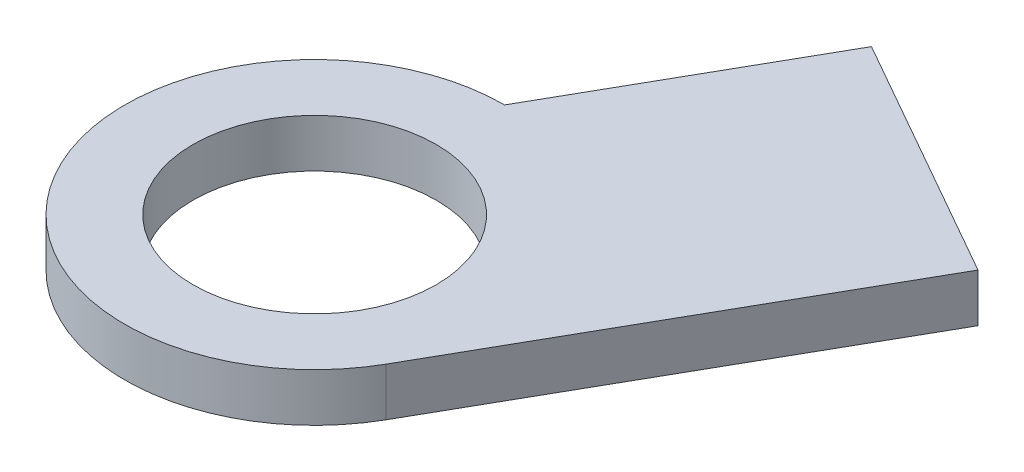
SolidWorks part; units mm, degrees
ref_plane "Front Plane" through (0, 0, 0) normal (0, 0, 1) x (1, 0, 0)
ref_plane "Top Plane" through (0, 0, 0) normal (0, 1, 0) x (1, 0, 0)
ref_plane "Right Plane" through (0, 0, 0) normal (1, 0, 0) x (0, 0, -1)
sketch "Sketch1" plane through (0, 0, 0) normal (0, 1, 0) x (1, 0, 0)
  circle A0 centre (0, 0) radius 12.5
  dimension "D2" = 25
extrude "Boss-Extrude1" add sketch "Sketch1" along normal blind 17.6
sketch "Sketch2" plane through (0, 17.6, 0) normal (0, 1, 0) x (1, 0, 0)
  circle A0 centre (0, 0) radius 5.5
  dimension "D1" = 11
extrude "Cut-Extrude1" cut sketch "Sketch2" against normal blind 50.8
sketch "Sketch3" plane through (0, 17.6, 0) normal (0, 1, 0) x (1, 0, 0)
  circle A0 centre (0, 0) radius 8
  dimension "D1" = 16
extrude "Cut-Extrude3" cut sketch "Sketch3" against normal offset from surface (15.6 mm away) 2 up to face at (0, 0, 5.5)
sketch "Sketch4" plane through (0, 17.6, 0) normal (0, 1, 0) x (1, 0, 0)
  line L0 (0, 0) -> (0, 26.4023)
  line L1 (0, 0) -> (-26.3638, 0)
  circle A0 centre (0, 0) radius 8 construction
  circle A1 centre (0, 0) radius 12.5 construction
  circle A2 centre (0, 0) radius 8
  circle A3 centre (0, 0) radius 12.5
  circle M3 centre (0, 0) radius 8
  circle M4 centre (0, 0) radius 12.5
  dimension "D1" = 90
extrude "Cut-Extrude4" [suppressed] cut sketch "Sketch4" against normal through all contours L1 L0 M3 M4
sketch "Sketch5" plane through (0, 17.6, 0) normal (0, 1, 0) x (1, 0, 0)
  line L1 (10.868, -6.1756) -> (24.9853, 18.6686)
  line L2 (24.9853, 18.6686) -> (8.7481, 27.8951)
  line L3 (8.7481, 27.8951) -> (0, 12.5)
  circle A0 centre (0, 0) radius 12.5 construction
  point P0 (0, 0)
  dimension "D1" = 28.575
  dimension "D2" = 18.6756
extrude "Boss-Extrude2" add sketch "Sketch5" against normal through all
fillet "Fillet1" [suppressed] radius 2
sketch "Sketch6" plane through (0, 0, 0) normal (0, -1, 0) x (1, 0, 0)
  line L3 (0, -12.5) -> (8.7481, -27.8951)
  line L4 (8.7481, -27.8951) -> (24.9853, -18.6686)
  line L5 (24.9853, -18.6686) -> (10.868, 6.1756)
  line L6 (0, -12.5) -> (8.7481, -27.8951)
  line L7 (8.7481, -27.8951) -> (24.9853, -18.6686)
  line L8 (24.9853, -18.6686) -> (10.868, 6.1756)
  circle A0 centre (0, 0) radius 8 construction
  arc A1 (10.868, 6.1756) -> (0, -12.5) centre (0, 0) ccw
  arc A2 (10.868, 6.1756) -> (0, -12.5) centre (0, 0) ccw
  circle A3 centre (0, 0) radius 8
  circle M5 centre (0, 0) radius 5.5
  arc M6 (10.868, 6.1756) -> (0, -12.5) centre (0, 0) ccw
  line M7 (0, -12.5) -> (8.7481, -27.8951)
  line M8 (8.7481, -27.8951) -> (24.9853, -18.6686)
  line M9 (24.9853, -18.6686) -> (10.868, 6.1756)
  dimension "D1" = 0
extrude "Cut-Extrude5" cut sketch "Sketch6" against normal offset from surface (14.425 mm away) 3.175 contours A3 M5 | A3 M9 M6 M7 M8 up to face at (0, 17.6, 8)
equation "\"1.1c\"=0.0104601"
